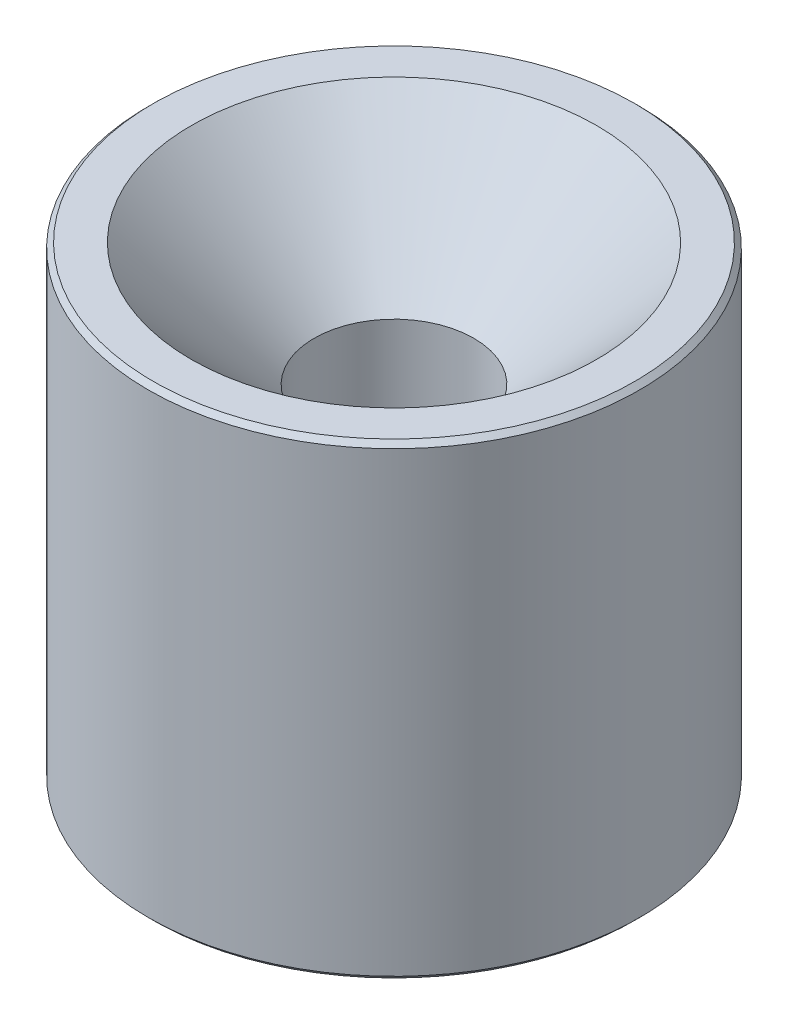
SolidWorks part; units mm, degrees
material "POM Acetal Copolymer"
ref_plane "Front Plane" through (0, 0, 0) normal (0, 0, 1) x (1, 0, 0)
ref_plane "Top Plane" through (0, 0, 0) normal (0, 1, 0) x (1, 0, 0)
ref_plane "Right Plane" through (0, 0, 0) normal (1, 0, 0) x (0, 0, -1)
sketch "Sketch1" plane through (0, 0, 0) normal (0, 0, 1) x (1, 0, 0)
  line L0 (3.45, -9.5) -> (9.8, -9.5)
  line L1 (9.8, -9.5) -> (10, -9.3)
  line L2 (10, -9.3) -> (10, 9.3)
  line L3 (10, 9.3) -> (9.8, 9.5)
  line L4 (9.8, 9.5) -> (8.25, 9.5)
  line L5 (8.25, 9.5) -> (3.25, 4.5)
  line L6 (3.25, 4.5) -> (3.25, -9.3)
  line L7 (3.25, -9.3) -> (3.45, -9.5)
  line L8 (0, 9.5) -> (0, -9.5) construction
  dimension "D1" = 6.5
  dimension "D2" = 20
  dimension "D3" = 19
  dimension "D4" = 14
  dimension "D5" = 9.5
  dimension "D6" = 45
  dimension "D7" = 0.2
  dimension "D8" = 0.2
  dimension "D9" = 0.2
  dimension "D10" = 0.2
revolve "Revolve1" add sketch "Sketch1" angle 360 about L8
